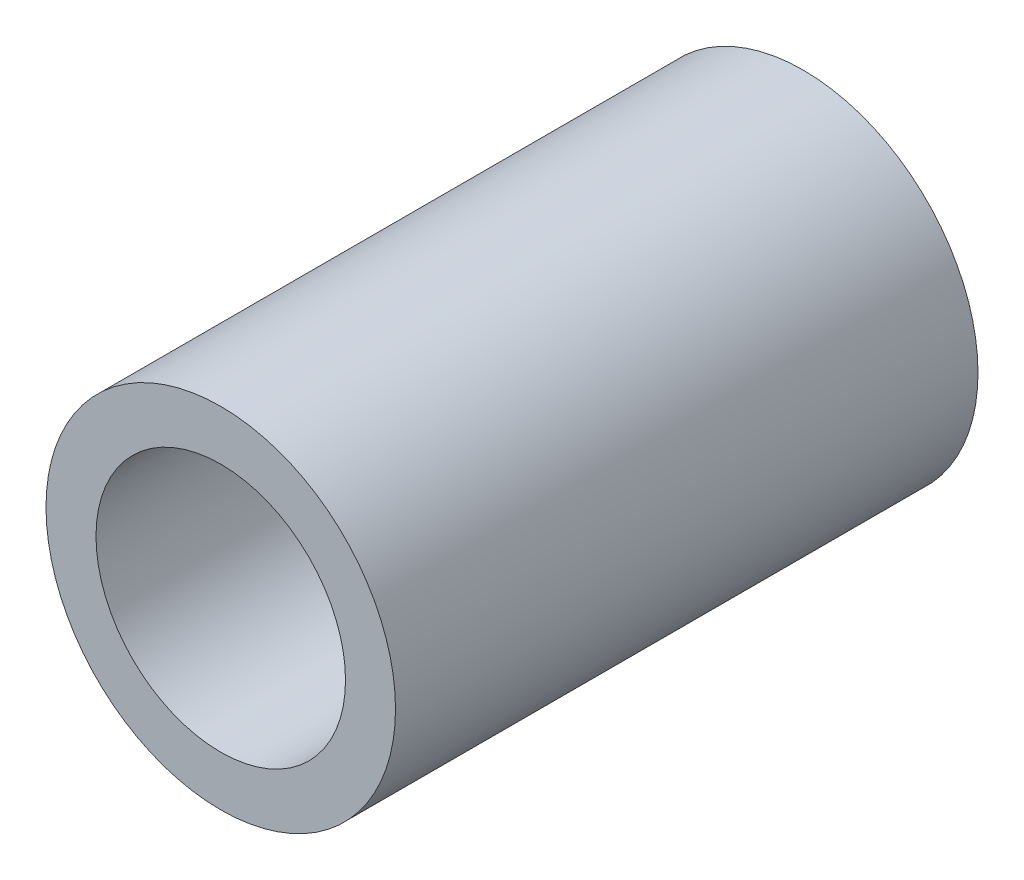
SolidWorks part; units mm, degrees
material "ABS"
ref_plane "Front Plane" through (0, 0, 0) normal (0, 0, 1) x (1, 0, 0)
ref_plane "Top Plane" through (0, 0, 0) normal (0, 1, 0) x (1, 0, 0)
ref_plane "Right Plane" through (0, 0, 0) normal (1, 0, 0) x (0, 0, -1)
sketch "Sketch1" plane through (0, 0, 0) normal (0, 0, 1) x (1, 0, 0)
  circle A0 centre (0, 0) radius 1.7
  circle A1 centre (0, 0) radius 2.3813
  dimension "D1" = 3.4
  dimension "D2" = 4.7625
extrude "Boss-Extrude1" add sketch "Sketch1" along normal mid plane 7.9375
